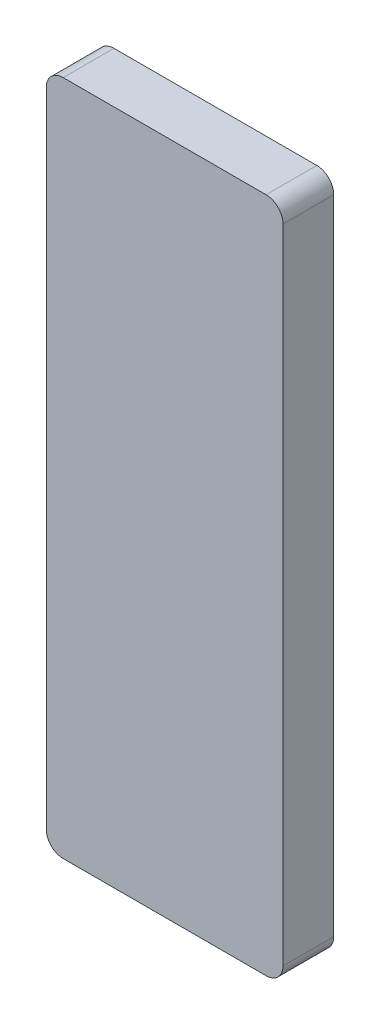
SolidWorks part; units mm, degrees
material "Cèdre"
ref_plane "Plan de face" through (0, 0, 0) normal (0, 0, 1) x (1, 0, 0)
ref_plane "Plan de dessus" through (0, 0, 0) normal (0, 1, 0) x (1, 0, 0)
ref_plane "Plan de droite" through (0, 0, 0) normal (1, 0, 0) x (0, 0, -1)
sketch "Esquisse1" plane through (0, 0, 0) normal (0, 0, 1) x (1, 0, 0)
  line L0 (0, 60) -> (0, -60) construction
  line L1 (-21, 60) -> (21, 60)
  line L2 (-21, 60) -> (-21, -60)
  line L3 (-21, -60) -> (21, -60)
  line L4 (21, 60) -> (21, -60)
  line L6 (21, 0) -> (-21, 0) construction
  line L7 (-21, 0) -> (21, 0) construction
  dimension "D1" = 120
  dimension "D2" = 42
extrude "Boss.-Extru.1" add sketch "Esquisse1" along normal blind 9
fillet "Congé1" radius 3 4 edges at (-21, -60, 4.5) (21, -60, 4.5) (21, 60, 4.5) (-21, 60, 4.5)
